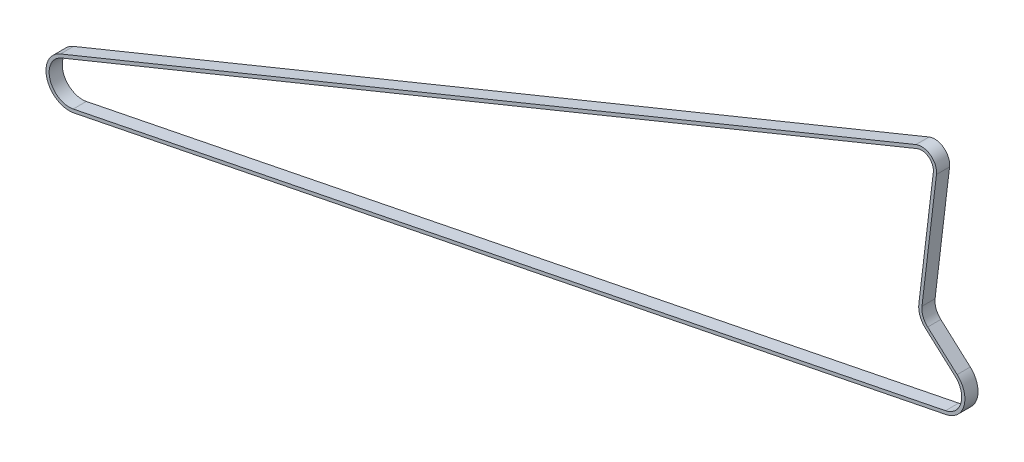
SolidWorks part; units mm, degrees
material "NEOPRENE"
ref_plane "Front Plane" through (0, 0, 0) normal (0, 0, 1) x (1, 0, 0)
ref_plane "Top Plane" through (0, 0, 0) normal (0, 1, 0) x (1, 0, 0)
ref_plane "Right Plane" through (0, 0, 0) normal (1, 0, 0) x (0, 0, -1)
sketch "Sketch2" plane through (0, 0, 0) normal (0, 0, 1) x (1, 0, 0)
  line L0 (0, 0) -> (1, 0) construction
  line L1 (0, 0) -> (0, 1) construction
  line L2 (6.634, 7.3924) -> (-6.8441, 19.4878)
  line L3 (-9.6884, 27.0366) -> (-3.0657, 82.5449)
  line L4 (-11.466, 88.9437) -> (-402.7543, -70.8042)
  line L5 (-397.0474, -89.7388) -> (1.9526, -9.7388)
  arc A0 (1.9526, -9.7388) -> (6.634, 7.3924) centre (0, 0) ccw
  arc A1 (-6.8441, 19.4878) -> (-9.6884, 27.0366) centre (-1, 26) cw
  arc A2 (-3.0657, 82.5449) -> (-11.466, 88.9437) centre (-9.15, 83.2708) ccw
  arc A3 (-402.7543, -70.8042) -> (-397.0474, -89.7388) centre (-399, -80) ccw
ref_plane "Plane1" through (1.9526, -9.7388, 0) normal (0.1966, -0.9805, 0) x (0.9805, 0.1966, 0)
ref_plane "Plane2" through (0, 0, 0) normal (0, 0, -1) x (0.9805, 0.1966, 0)
sketch "Sketch3" plane through (1.9526, -9.7388, 0) normal (0.1966, -0.9805, 0) x (0.9805, 0.1966, 0)
  line L0 (0, 0) -> (0, 22.3341) construction
ref_plane "Plane3" through (0, 0, 0) normal (0.9805, 0.1966, 0) x (0, 0, 1)
sketch "Sketch4" plane through (0, 0, 0) normal (0.9805, 0.1966, 0) x (0, 0, 1)
  line L0 (-3, 10.6577) -> (-3, 9.2077)
  line L1 (-3, 10.6577) -> (3, 10.6577)
  line L2 (-3, 9.2077) -> (3, 9.2077)
  line L3 (3, 10.6577) -> (3, 9.2077)
  line L4 (-3, 10.6577) -> (3, 9.2077) construction
  line L5 (-3, 9.2077) -> (3, 10.6577) construction
  point P1 (0, 9.9327)
  dimension "D1" = 1.45
  dimension "D2" = 6
sweep "Sweep1" add profiles "Sketch4" path "Sketch2"
